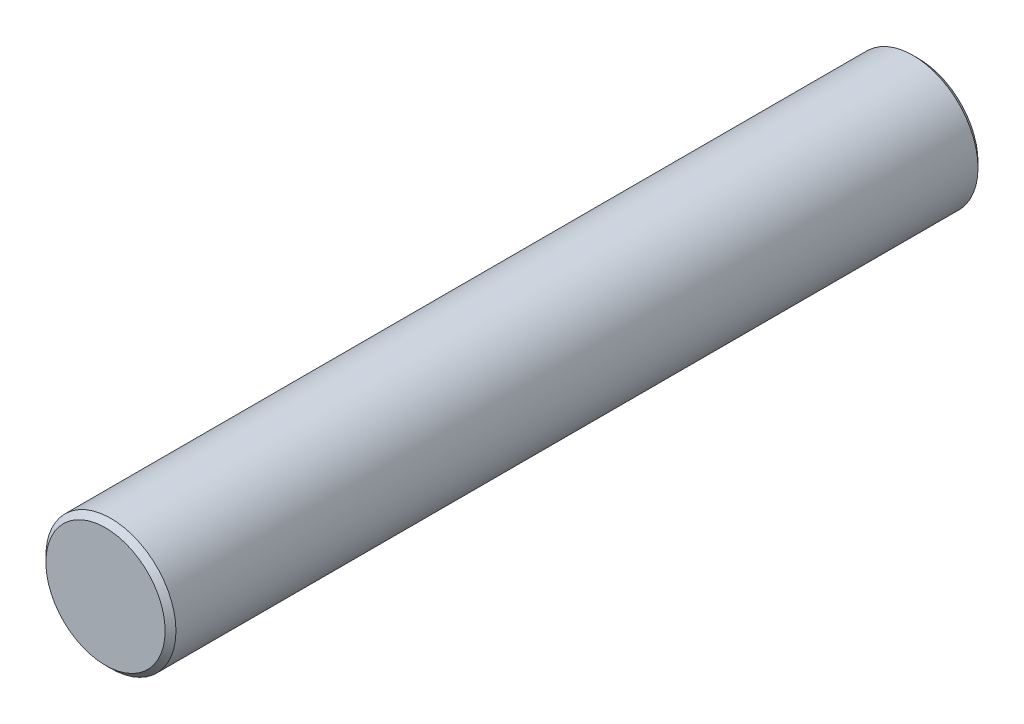
SolidWorks part; units mm, degrees
ref_plane "Front Plane" through (0, 0, 0) normal (0, 0, 1) x (1, 0, 0)
ref_plane "Top Plane" through (0, 0, 0) normal (0, 1, 0) x (1, 0, 0)
ref_plane "Right Plane" through (0, 0, 0) normal (1, 0, 0) x (0, 0, -1)
sketch "스케치1" plane through (0, 0, 0) normal (0, 1, 0) x (1, 0, 0)
  line L0 (5.5, 0) -> (0, 0)
  line L1 (0, 0) -> (0, -75)
  line L2 (0, -75) -> (5.5, -75)
  line L3 (5.5, -75) -> (6, -74.5)
  line L4 (6, -74.5) -> (6, -0.5)
  line L5 (6, -0.5) -> (5.5, 0)
  line L6 (0, 0) -> (0, -75) construction
revolve "회전1" add sketch "스케치1" angle 360 about L6
